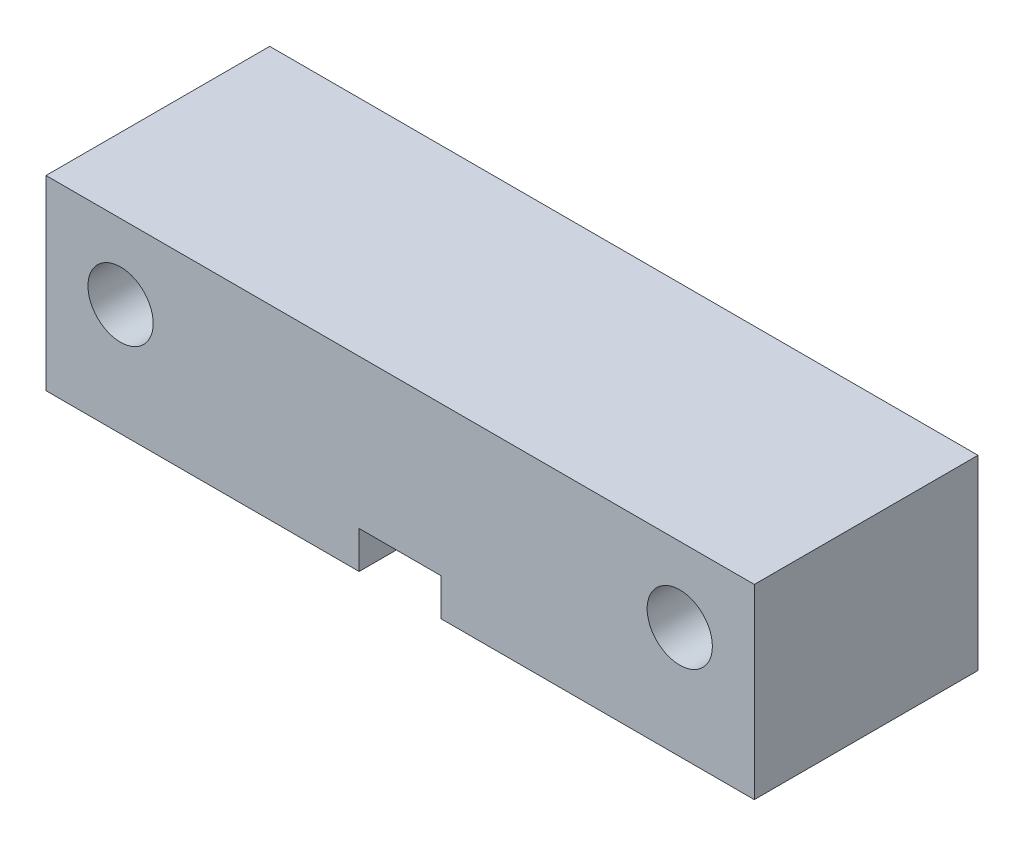
SolidWorks part; units mm, degrees
ref_plane "Front" through (0, 0, 0) normal (0, 0, 1) x (1, 0, 0)
ref_plane "Top" through (0, 0, 0) normal (0, 1, 0) x (1, 0, 0)
ref_plane "Right" through (0, 0, 0) normal (1, 0, 0) x (0, 0, -1)
sketch "Sketch1" plane through (0, 0, 0) normal (0, 0, 1) x (1, 0, 0)
  line L0 (0, 1) -> (11498.3442, 1) construction
  line L1 (-19, 5) -> (19, 5)
  line L2 (-19, 5) -> (-19, -5)
  line L3 (-19, -5) -> (19, -5)
  line L4 (19, 5) -> (19, -5)
  line L5 (-19, 5) -> (19, -5) construction
  line L6 (-19, -5) -> (19, 5) construction
  line L7 (0, 0) -> (0, 11498.3442) construction
  circle A0 centre (15, 1) radius 1.75
  circle A1 centre (-15, 1) radius 1.75
  point P0 (0, 0)
  point P15 (0, 5)
  dimension "D1" = 3.5
  dimension "D2" = 10
  dimension "D3" = 38
  dimension "D4" = 30
  dimension "D5" = 4
extrude "Boss-Extrude1" add sketch "Sketch1" along normal blind 12
sketch "Sketch2" plane through (0, -5, 0) normal (0, -1, 0) x (1, 0, 0)
  line L0 (-19, 6) -> (49981, 6) construction
  line L1 (-19, 12) -> (-19, 0) construction
  line L2 (19, 12) -> (19, 0) construction
  line L3 (0, 12) -> (0, -49988) construction
  line L4 (-19, 12) -> (19, 12) construction
  line L7 (2.2, -0.05) -> (2.2, 2.8316)
  line L10 (2.2, 2.8316) -> (14.5498, 4.2111)
  line L11 (14.5498, 7.7889) -> (2.2, 9.1684)
  line L12 (2.2, 9.1684) -> (2.2, 12.75)
  line L31 (-2.2, 12.75) -> (-2.2, 9.7139)
  line L32 (-2.2, 9.7139) -> (-17.1798, 7.7853)
  line L33 (-17.1798, 4.2147) -> (-2.2, 2.2861)
  line L34 (-2.2, 2.2861) -> (-2.2, -0.05)
  line L35 (1.9, -0.05) -> (1.9, 3.0105)
  line L36 (1.9889, 3.1099) -> (14.5165, 4.5093)
  line L37 (14.5165, 7.4907) -> (1.9889, 8.8901)
  line L38 (1.9, 8.9895) -> (1.9, 12.75)
  line L39 (-1.9, 12.75) -> (-1.9, 9.538)
  line L40 (-1.9872, 9.4388) -> (-17.1415, 7.4877)
  line L41 (-17.1415, 4.5123) -> (-1.9872, 2.5612)
  line L42 (-1.9, 2.462) -> (-1.9, -0.05)
  line L43 (1.9, -0.05) -> (1.9, 3.0105) construction
  line L44 (1.9889, 3.1099) -> (14.5165, 4.5093) construction
  line L45 (14.5165, 7.4907) -> (1.9889, 8.8901) construction
  line L46 (1.9, 8.9895) -> (1.9, 12.75) construction
  line L47 (-1.9, 12.75) -> (-1.9, 9.538) construction
  line L48 (-1.9872, 9.4388) -> (-17.1415, 7.4877) construction
  line L49 (-17.1415, 4.5123) -> (-1.9872, 2.5612) construction
  line L50 (-1.9, 2.462) -> (-1.9, -0.05) construction
  circle A0 centre (0, 6) radius 3.9
  arc A3 (2.2, 2.8316) -> (2.2, 2.8316) centre (2.2, 2.8316) ccw
  arc A4 (14.5498, 4.2111) -> (14.5498, 7.7889) centre (14.35, 6) ccw
  arc A14 (2.2, 9.1684) -> (2.2, 9.1684) centre (2.2, 9.1684) ccw
  arc A17 (2.2, 12.75) -> (-2.2, 12.75) centre (0, 12.75) ccw
  arc A18 (-2.2, 9.7139) -> (-2.2, 9.7139) centre (-2.2, 9.7139) ccw
  arc A19 (-17.1798, 7.7853) -> (-17.1798, 4.2147) centre (-16.95, 6) ccw
  arc A20 (-2.2, 2.2861) -> (-2.2, 2.2861) centre (-2.2, 2.2861) ccw
  arc A21 (-2.2, -0.05) -> (2.2, -0.05) centre (0, -0.05) ccw
  arc A22 (1.9889, 3.1099) -> (1.9, 3.0105) centre (2, 3.0105) ccw
  arc A23 (14.5165, 4.5093) -> (14.5165, 7.4907) centre (14.35, 6) ccw
  arc A24 (1.9, 8.9895) -> (1.9889, 8.8901) centre (2, 8.9895) ccw
  arc A25 (1.9, 12.75) -> (-1.9, 12.75) centre (0, 12.75) ccw
  arc A26 (-1.9872, 9.4388) -> (-1.9, 9.538) centre (-2, 9.538) ccw
  arc A27 (-17.1415, 7.4877) -> (-17.1415, 4.5123) centre (-16.95, 6) ccw
  arc A28 (-1.9, 2.462) -> (-1.9872, 2.5612) centre (-2, 2.462) ccw
  arc A29 (-1.9, -0.05) -> (1.9, -0.05) centre (0, -0.05) ccw
  arc A30 (1.9889, 3.1099) -> (1.9, 3.0105) centre (2, 3.0105) ccw construction
  arc A31 (14.5165, 4.5093) -> (14.5165, 7.4907) centre (14.35, 6) ccw construction
  arc A32 (1.9, 8.9895) -> (1.9889, 8.8901) centre (2, 8.9895) ccw construction
  arc A33 (1.9, 12.75) -> (-1.9, 12.75) centre (0, 12.75) ccw construction
  arc A34 (-1.9872, 9.4388) -> (-1.9, 9.538) centre (-2, 9.538) ccw construction
  arc A35 (-17.1415, 7.4877) -> (-17.1415, 4.5123) centre (-16.95, 6) ccw construction
  arc A36 (-1.9, 2.462) -> (-1.9872, 2.5612) centre (-2, 2.462) ccw construction
  arc A37 (-1.9, -0.05) -> (1.9, -0.05) centre (0, -0.05) ccw construction
  point P4 (-19, 6)
  point P7 (19, 6)
  point P12 (0, 12)
  point P14 (0, 6)
  point P21 (17.5, 6)
  point P33 (0, -0.7599)
  point P34 (0, -0.8079)
  dimension "D1" = 7.8
  dimension "D2" = 17.5
  dimension "D3" = 0
  dimension "D4" = 0.3
extrude "Cut-Extrude3" cut sketch "Sketch2" against normal blind 2 contours L32 A19 L33 A20 L34 A21 L7 A3 L10 A4 L11 A14 L12 A17 L31 A18
